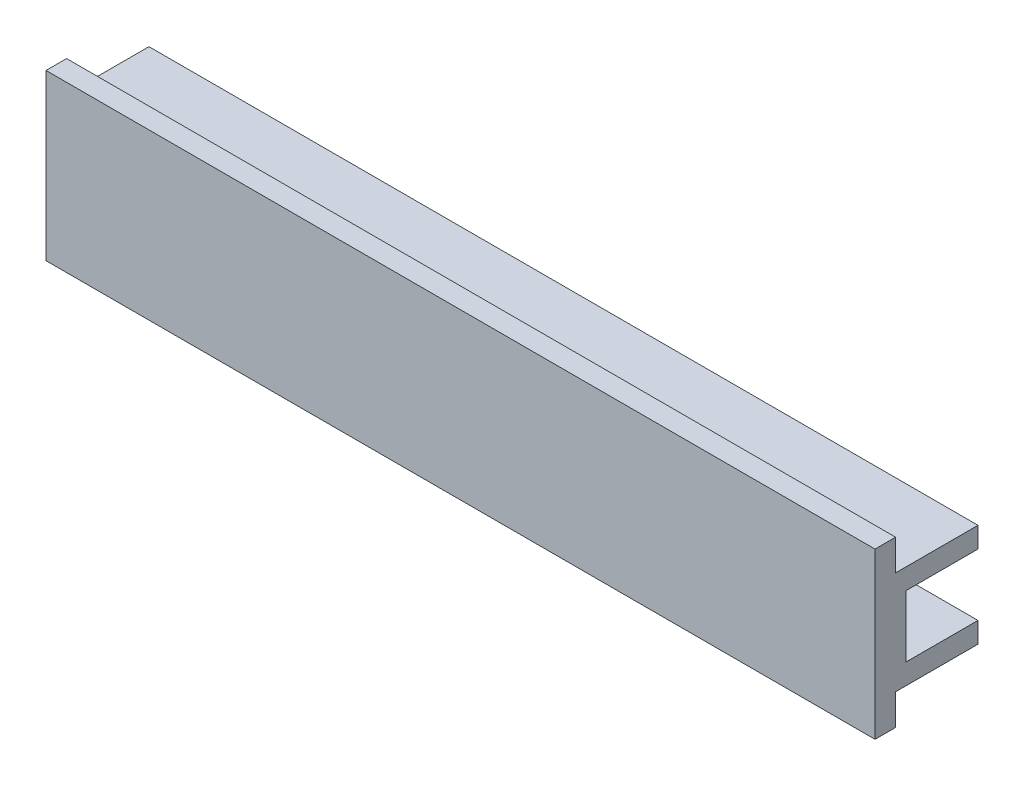
SolidWorks part; units mm, degrees
ref_plane "Front Plane" through (0, 0, 0) normal (0, 0, 1) x (1, 0, 0)
ref_plane "Top Plane" through (0, 0, 0) normal (0, 1, 0) x (1, 0, 0)
ref_plane "Right Plane" through (0, 0, 0) normal (1, 0, 0) x (0, 0, -1)
sketch "Sketch1" plane through (0, 0, 0) normal (1, 0, 0) x (0, 0, -1)
  line L0 (-3, 8) -> (-3, 5)
  line L1 (-5, 8) -> (-3, 8)
  line L2 (-5, 8) -> (-5, -8)
  line L3 (-5, -8) -> (-3, -8)
  line L4 (5, 5) -> (5, 3)
  line L5 (-5, 8) -> (5, -8) construction
  line L6 (-5, -8) -> (5, 8) construction
  line L7 (-3, 5) -> (5, 5)
  line L8 (5, 3) -> (-2, 3)
  line L9 (-2, 3) -> (-2, -3)
  line L10 (-2, -3) -> (5, -3)
  line L11 (5, -5) -> (-3, -5)
  line L12 (-3, -5) -> (-3, -8)
  line L13 (5, -3) -> (5, -5)
  point P0 (0, 0)
  dimension "D1" = 16
  dimension "D2" = 10
  dimension "D3" = 2
  dimension "D4" = 2
  dimension "D5" = 2
  dimension "D6" = 6
  dimension "D7" = 3
  dimension "D8" = 7
  dimension "D9" = 10
  dimension "D10" = 5
extrude "Extrude1" add sketch "Sketch1" along normal mid plane 80.5
sketch "Sketch2" plane through (-40.25, 0, 0) normal (-1, 0, 0) x (0, 0, 1)
  line L0 (2, 3) -> (3, 3)
  line L1 (3, 3) -> (3, -3)
  line L2 (3, -3) -> (2, -3)
  line L3 (2, -3) -> (2, 3)
  dimension "D1" = 1
extrude "Extrude2" cut sketch "Sketch2" against normal blind 22
sketch "Sketch3" plane through (0, 0, 2) normal (0, 0, -1) x (-1, 0, 0)
  line L0 (18.25, 3) -> (18.25, -3) construction
  line L1 (18.25, 3) -> (18.25, -3)
  arc A0 (18.25, 3) -> (18.25, -3) centre (18.25, 0) ccw
extrude "Extrude3" cut sketch "Sketch3" against normal up to surface (1 mm away) up to face at (-29.25, 0, 3)
